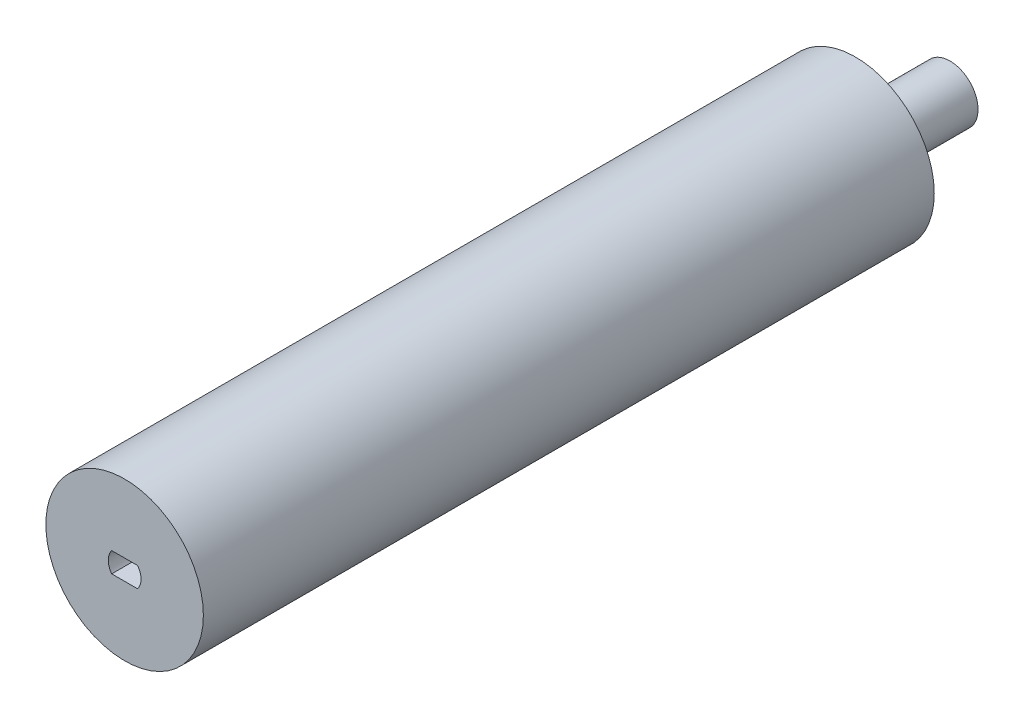
SolidWorks part; units mm, degrees
ref_plane "Front Plane" through (0, 0, 0) normal (0, 0, 1) x (1, 0, 0)
ref_plane "Top Plane" through (0, 0, 0) normal (0, 1, 0) x (1, 0, 0)
ref_plane "Right Plane" through (0, 0, 0) normal (1, 0, 0) x (0, 0, -1)
sketch "Sketch1" plane through (0, 0, 0) normal (0, 0, 1) x (1, 0, 0)
  line L10 (2.0511, -1.5674) -> (-2.0477, -1.5674)
  line L11 (2.0511, 1.6326) -> (-2.0477, 1.6326)
  arc A12 (-2.0477, 1.6326) -> (-2.0477, -1.5674) centre (0.0017, 0.0326) ccw
  arc A13 (2.0511, -1.5674) -> (2.0511, 1.6326) centre (0.0017, 0.0326) ccw
  point P8 (0, 1.5)
  point P11 (0, -1.5)
sketch "Sketch2" plane through (0, 0, 0) normal (0, 0, 1) x (1, 0, 0)
  circle A0 centre (0, 0) radius 12.5
  dimension "D1" = 25
extrude "Boss-Extrude1" add sketch "Sketch2" against normal blind 116
sketch "Sketch3" plane through (0, 0, -116) normal (0, 0, -1) x (-1, 0, 0)
  circle A0 centre (0, 0) radius 4.45
  dimension "D1" = 8.9
extrude "Boss-Extrude2" add sketch "Sketch3" along normal blind 15
extrude "Cut-Extrude1" cut sketch "Sketch1" against normal blind 10
